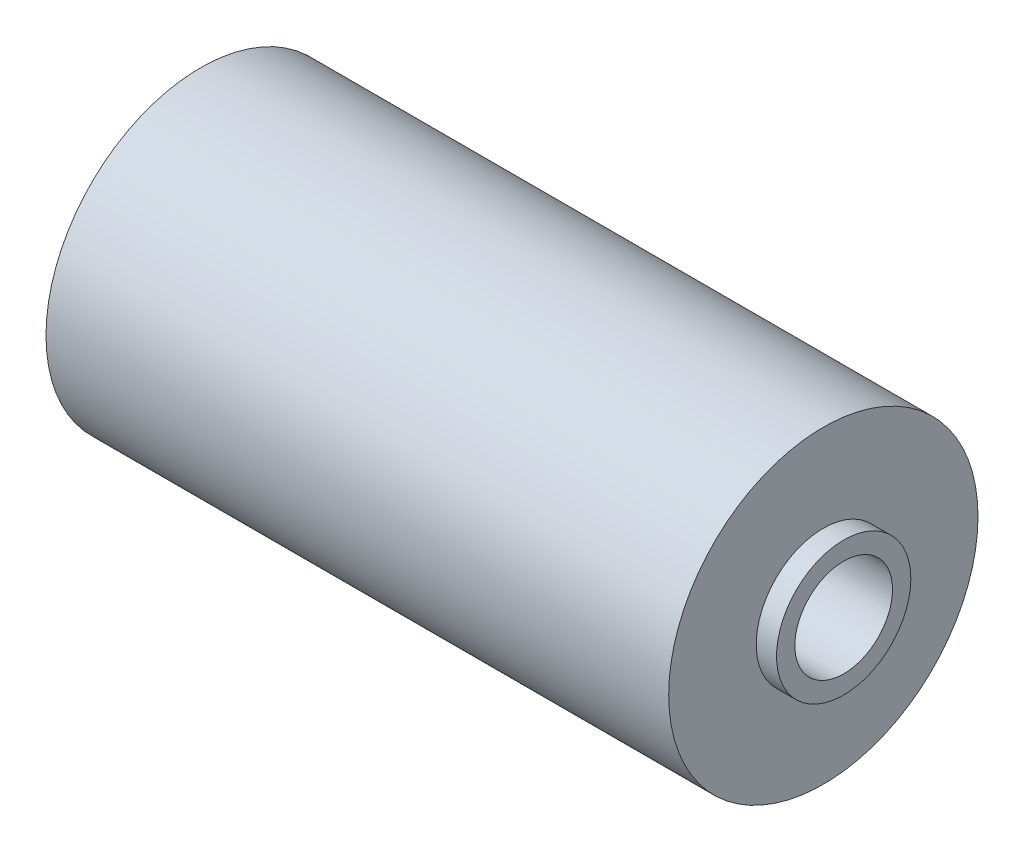
SolidWorks part; units mm, degrees
ref_plane "Front Plane" through (0, 0, 0) normal (0, 0, 1) x (1, 0, 0)
ref_plane "Top Plane" through (0, 0, 0) normal (0, 1, 0) x (1, 0, 0)
ref_plane "Right Plane" through (0, 0, 0) normal (1, 0, 0) x (0, 0, -1)
sketch "Sketch1" plane through (0, 0, 0) normal (1, 0, 0) x (0, 0, -1)
  circle A0 centre (0, 0) radius 12
  circle A1 centre (0, 0) radius 16.5
  dimension "D1" = 33
  dimension "D2" = 24
extrude "Boss-Extrude1" add sketch "Sketch1" along normal mid plane 163
sketch "Sketch2" plane through (-81.5, 0, 0) normal (-1, 0, 0) x (0, 0, 1)
  circle A0 centre (0, 0) radius 38
  dimension "D1" = 76
extrude "Boss-Extrude2" add sketch "Sketch2" against normal offset from surface (153 mm away) 5 from offset 5 up to face at (81.5, 0, -16.5) offset against normal yes
sketch "Sketch3" plane through (-76.5, 0, 0) normal (-1, 0, 0) x (0, 0, 1)
  circle A1 centre (0, 0) radius 12
  circle A2 centre (0, 0) radius 12
  dimension "D1" = 0
extrude "Cut-Extrude1" cut sketch "Sketch3" against normal through all both and the other way through all
